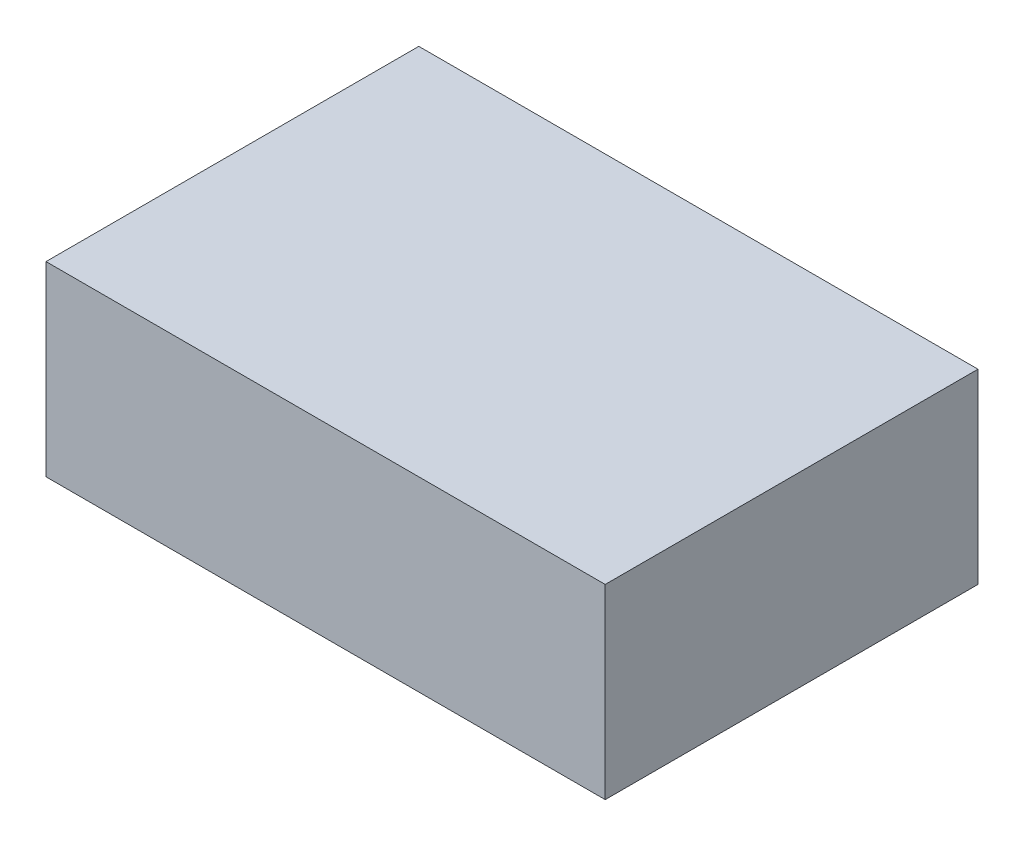
SolidWorks part; units mm, degrees
material "PC High Viscosity"
ref_plane "Front Plane" through (0, 0, 0) normal (0, 0, 1) x (1, 0, 0)
ref_plane "Top Plane" through (0, 0, 0) normal (0, 1, 0) x (1, 0, 0)
ref_plane "Right Plane" through (0, 0, 0) normal (1, 0, 0) x (0, 0, -1)
sketch "BaseS" plane through (0, 0, 0) normal (0, 1, 0) x (1, 0, 0)
  line L1 (-0.6, 0.4) -> (0.6, 0.4)
  line L2 (-0.6, 0.4) -> (-0.6, -0.4)
  line L3 (-0.6, -0.4) -> (0.6, -0.4)
  line L4 (0.6, 0.4) -> (0.6, -0.4)
  line L5 (-0.6, 0.4) -> (0.6, -0.4) construction
  line L6 (-0.6, -0.4) -> (0.6, 0.4) construction
  point P0 (0, 0)
  dimension "Width" = 1.2
  dimension "Length" = 0.8
extrude "Base" add sketch "BaseS" along normal blind 0.4
